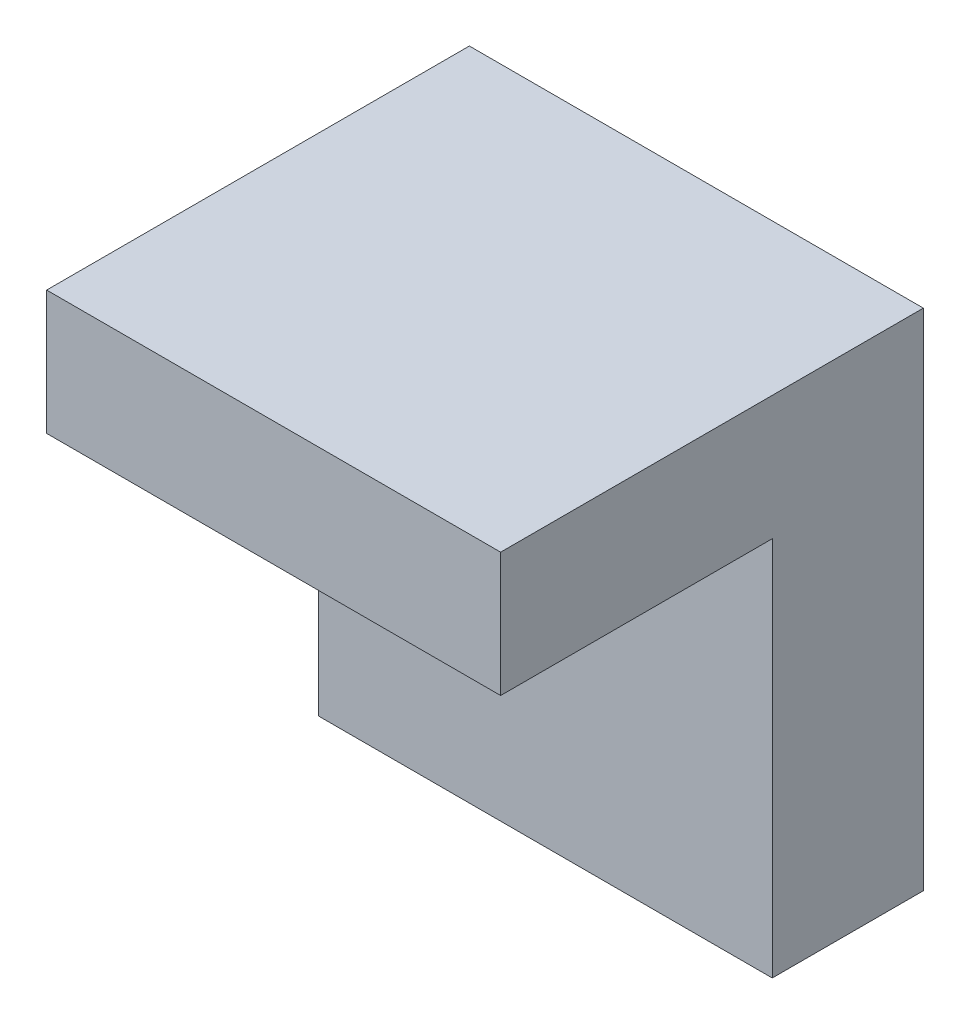
SolidWorks part; units mm, degrees
ref_plane "Front Plane" through (0, 0, 0) normal (0, 0, 1) x (1, 0, 0)
ref_plane "Top Plane" through (0, 0, 0) normal (0, 1, 0) x (1, 0, 0)
ref_plane "Right Plane" through (0, 0, 0) normal (1, 0, 0) x (0, 0, -1)
sketch "Sketch1" plane through (0, 0, 0) normal (1, 0, 0) x (0, 0, -1)
  line L1 (3.5, -1.6) -> (-3.5, -1.6)
  line L2 (3.5, -1.6) -> (3.5, 1.6)
  line L3 (3.5, 1.6) -> (-3.5, 1.6)
  line L4 (-3.5, -1.6) -> (-3.5, 1.6)
  line L5 (3.5, -1.6) -> (-3.5, 1.6) construction
  line L6 (3.5, 1.6) -> (-3.5, -1.6) construction
  line L7 (3.5, 1.6) -> (7.3936, 1.6)
  line L8 (3.5, 1.6) -> (3.5, -11.4043)
  line L9 (3.5, -11.4043) -> (7.3936, -11.4043)
  line L10 (7.3936, 1.6) -> (7.3936, -11.4043)
  point P0 (0, 0)
  dimension "D1" = 3.2
  dimension "D2" = 7
extrude "Boss-Extrude1" add sketch "Sketch1" along normal blind 11.7 contours L10 L3 L4 L1 | L1 L10 L9 L8 | L3 L10 L1 L2
